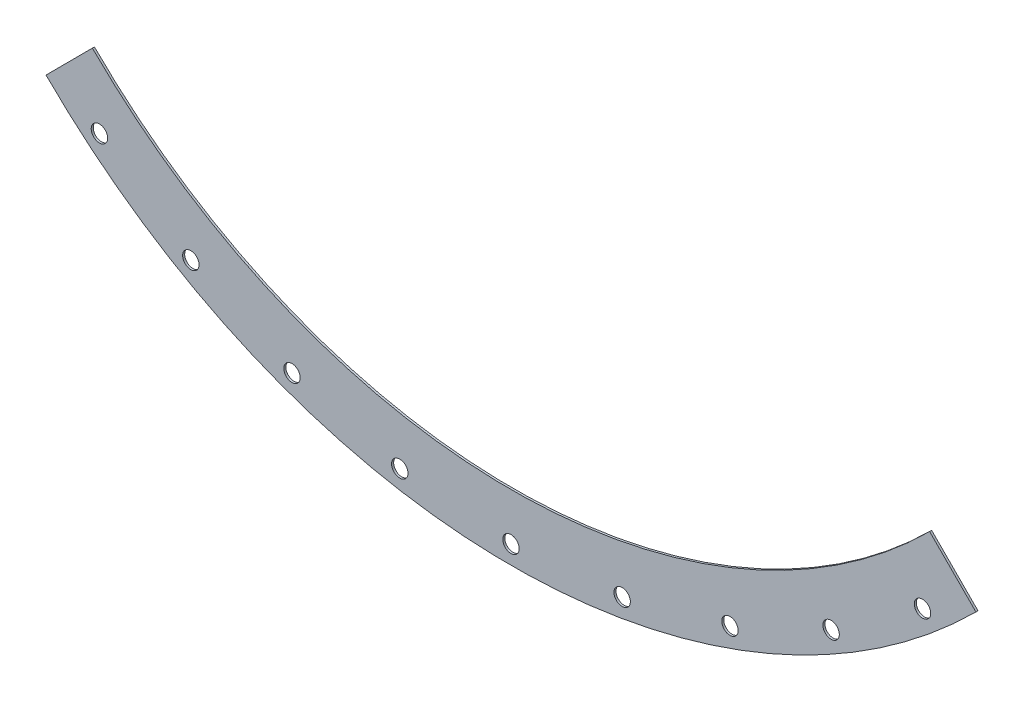
SolidWorks part; units mm, degrees
material "6061-T6 Al"
ref_plane "Front" through (0, 0, 0) normal (0, 0, 1) x (1, 0, 0)
ref_plane "Top" through (0, 0, 0) normal (0, 1, 0) x (1, 0, 0)
ref_plane "Right" through (0, 0, 0) normal (1, 0, 0) x (0, 0, -1)
sketch "Sketch" plane through (0, 0, 0) normal (0, 0, 1) x (1, 0, 0)
  line L0 (-647.6901, -649.9549) -> (-719.4067, -721.9223)
  line L2 (495.3, -857.8848) -> (458.7875, -794.6433) construction
  line L3 (338.8052, -930.8595) -> (313.8291, -862.2385) construction
  line L4 (172.0159, -975.5506) -> (159.3352, -903.635) construction
  line L6 (0, -990.6) -> (0, -917.575) construction
  line L7 (-172.0159, -975.5506) -> (-159.3352, -903.635) construction
  line L8 (-338.8052, -930.8595) -> (-313.8291, -862.2385) construction
  line L9 (636.7454, -758.8436) -> (589.8058, -702.9032) construction
  line L10 (-495.3, -857.8848) -> (-458.7875, -794.6433) construction
  line L11 (-636.7454, -758.8436) -> (-589.8058, -702.9032) construction
  line L55 (0, 0) -> (0, -917.575) construction
  line L56 (648.8235, -648.8235) -> (720.6656, -720.6656) construction
  line L57 (647.6901, -649.9549) -> (719.4067, -721.9223)
  arc A0 (647.6901, -649.9549) -> (648.8235, -648.8235) centre (0, 0) ccw construction
  arc A2 (-719.4067, -721.9223) -> (719.4067, -721.9223) centre (0, 0) ccw
  arc A3 (-647.6901, -649.9549) -> (647.6901, -649.9549) centre (0, 0) ccw
  arc A21 (0, -990.6) -> (636.7454, -758.8436) centre (0, 0) ccw construction
  arc A22 (719.4067, -721.9223) -> (720.6656, -720.6656) centre (0, 0) ccw construction
  point P5 (-25.908, 20.828)
  point P6 (25.908, 20.828)
  point P7 (25.908, -20.828)
  point P8 (-25.908, -20.828)
  point P48 (0, 0)
  point P63 (-25.781, -19.05)
  point P64 (25.781, -19.05)
  dimension "D5" = 2038.35
  dimension "D6" = 0.1
  dimension "D3" = 40
  dimension "D4" = 45
  dimension "D1" = 1981.2
  dimension "D2" = 1835.15
extrude "Boss-Extrude1" add sketch "Sketch" along normal blind 3.175
hole_wizard "1 (1) Diameter Hole1" positions "Sketch5" profile "Sketch4" hole size "1" standard "ANSI Inch" end condition through all
sketch "Sketch5" plane through (-384.9649, 41.3042, 3.175) normal (0, 0, 1) x (1, 0, 0)
  point P41 (1021.7103, -800.1479)
  point P44 (880.2649, -899.189)
  point P47 (723.77, -972.1637)
  point P50 (556.9808, -1016.8548)
  point P53 (384.9649, -1031.9042)
  point P56 (212.949, -1016.8548)
  point P59 (46.1597, -972.1637)
  point P62 (-110.3351, -899.189)
  point P65 (-251.7805, -800.1479)
sketch "Sketch4" plane through (636.7454, -758.8436, 3.175) normal (1, 0, 0) x (0, -1, 0)
  line L0 (0, 0) -> (0, 3.175)
  line L1 (0, 3.175) -> (12.7, 3.175)
  line L2 (12.7, 3.175) -> (12.7, 0)
  line L5 (12.7, 0) -> (0, 0)
  line L11 (0, -6.35) -> (0, 107.95) construction
  dimension "Thru Hole Dia." = 25.4
  dimension "Thru Hole Depth" = 3.175
